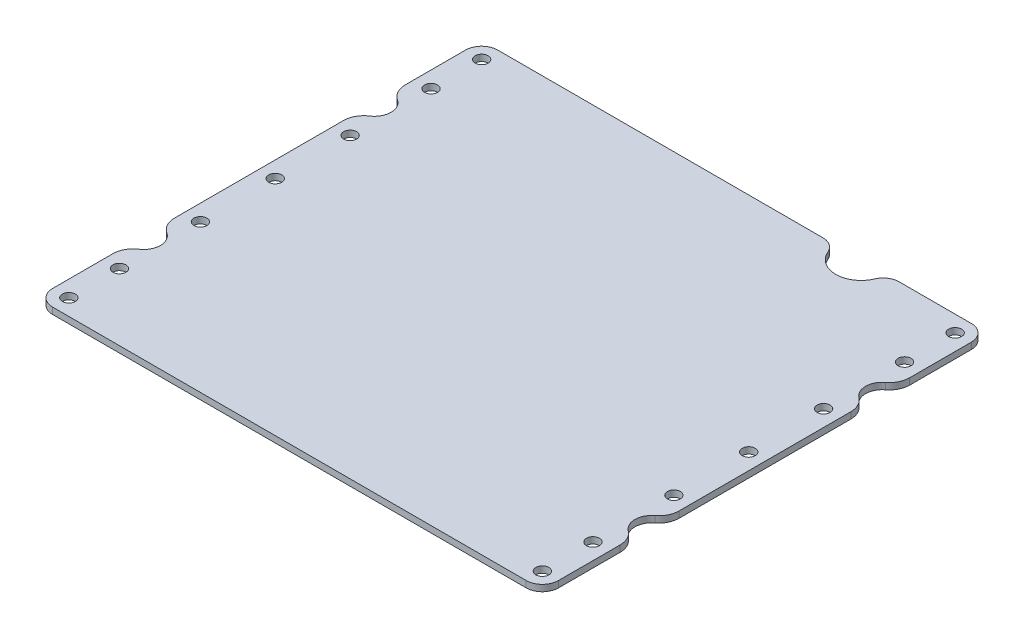
SolidWorks part; units mm, degrees
material "Glass"
ref_plane "Front Plane" through (0, 0, 0) normal (0, 0, 1) x (1, 0, 0)
ref_plane "Top Plane" through (0, 0, 0) normal (0, 1, 0) x (1, 0, 0)
ref_plane "Right Plane" through (0, 0, 0) normal (1, 0, 0) x (0, 0, -1)
sketch "Sketch1" plane through (0, 0, 0) normal (0, 1, 0) x (1, 0, 0)
  line L0 (0, -110) -> (0, 110) construction
  line L1 (-125, 110) -> (125, 110)
  line L2 (-125, 110) -> (-125, -110)
  line L3 (-125, -110) -> (125, -110)
  line L4 (125, 110) -> (125, -110)
  line L5 (0, 0) -> (125, 0) construction
  line L6 (-126.6867, 57) -> (126, 57) construction
  line L7 (-126, -57) -> (103.0564, -57) construction
  dimension "D1" = 250
  dimension "D2" = 220
extrude "Boss-Extrude1" add sketch "Sketch1" along normal blind 3.175
sketch "Sketch2" plane through (0, 3.175, 0) normal (0, 1, 0) x (-1, 0, 0)
  line L0 (0, 0) -> (0, -90.9285) construction
  line L1 (72.0845, 0) -> (-61.4496, 0) construction
  line L2 (117, 102) -> (117, -102) construction
  line L3 (97, 102) -> (97, -102) construction
  line L4 (-97, -102) -> (-97, 102) construction
  line L5 (-117, 102) -> (-117, -102) construction
  line L6 (117, -102) -> (-117, -102) construction
  line L7 (117, 102) -> (-117, 102) construction
  line L8 (-125, -110) -> (125, -110) construction
  line L9 (125, -110) -> (125, 110) construction
  line L10 (126, 57) -> (-134.8366, 57) construction
  circle A0 centre (117, -102) radius 3.2
  circle A1 centre (97, -102) radius 3.2 construction
  circle A2 centre (-97, -102) radius 3.2 construction
  circle A3 centre (-117, -102) radius 3.2
  circle A4 centre (-97, 102) radius 3.2 construction
  circle A5 centre (-117, 102) radius 3.2
  circle A6 centre (117, 102) radius 3.2
  circle A7 centre (97, 102) radius 3.2 construction
  circle A8 centre (117, -77) radius 3.2
  circle A9 centre (117, 77) radius 3.2
  circle A10 centre (-117, 77) radius 3.2
  circle A11 centre (-117, -77) radius 3.2
  circle A12 centre (117, 37) radius 3.2
  circle A13 centre (117, -37) radius 3.2
  circle A14 centre (-117, -37) radius 3.2
  circle A15 centre (-117, 37) radius 3.2
  dimension "D1" = 6.4
  dimension "D2" = 8
  dimension "D3" = 8
  dimension "D4" = 20
  dimension "D5" = 25
extrude "Cut-Extrude1" cut sketch "Sketch2" against normal through all
fillet "Fillet1" radius 8 4 edges at (-125, 1.5875, 110) (125, 1.5875, 110) (125, 1.5875, -110) (-125, 1.5875, -110)
sketch "Sketch4" plane through (0, 3.175, 0) normal (0, 1, 0) x (1, 0, 0)
  line L0 (117, 110) -> (-117, 110) construction
  line L1 (75, 110) -> (50, 110)
  line L2 (125, -102) -> (125, 102) construction
  arc A0 (50, 110) -> (75, 110) centre (62.5, 110) ccw
  dimension "D1" = 25
  dimension "D2" = 50
extrude "Cut-Extrude3" cut sketch "Sketch4" against normal through all
fillet "Fillet3" radius 8 2 edges at (75, 1.5875, -110) (50, 1.5875, -110)
sketch "Sketch5" plane through (0, 3.175, 0) normal (0, 1, 0) x (1, 0, 0)
  line L0 (-125, 57) -> (-117, 57) construction
  line L1 (-117, 77) -> (-117, 37) construction
  line L2 (-125, 102) -> (-125, -102) construction
  line L3 (-125, -57) -> (-116.75, -57) construction
  line L4 (125, -102) -> (125, 102) construction
  line L5 (108.6411, 70.2407) -> (117.7113, 53.1352)
  line L6 (125, -57) -> (115.662, -57) construction
  line L7 (112.3553, -72.0589) -> (111.8223, -72.5919)
  line L8 (108.6411, -70.2407) -> (117.7113, -53.1352)
  line L9 (112.3553, -72.0589) -> (125, -77.2965) construction
  line L10 (125, -77.2965) -> (125, -65.25)
  line L11 (108.3223, -74.6777) -> (126, -57) construction
  line L12 (0, 0) -> (107.8205, 0) construction
  line L13 (112.3553, 72.0589) -> (111.8223, 72.5919)
  line L14 (125, 77.2965) -> (125, 65.25)
  line L19 (108.3223, -74.6777) -> (118.6777, -74.6777) construction
  circle A0 centre (-125, 57) radius 8.25
  circle A1 centre (-125, -57) radius 8.25
  circle A2 centre (-117, -77) radius 3.2 construction
  circle A3 centre (-117, -37) radius 3.2 construction
  arc A4 (111.8223, 72.5919) -> (108.6411, 70.2407) centre (110.4081, 71.1777) ccw
  arc A5 (125, -65.25) -> (117.7113, -53.1352) centre (125, -57) ccw
  circle A8 centre (117, -77) radius 3.2 construction
  circle A9 centre (117, -37) radius 3.2 construction
  arc A10 (111.8223, -72.5919) -> (108.6411, -70.2407) centre (110.4081, -71.1777) cw
  arc A11 (112.3553, -72.0589) -> (125, -77.2965) centre (117.5929, -77.2965) cw
  circle A12 centre (126, -57) radius 4 construction
  arc A13 (112.3553, 72.0589) -> (125, 77.2965) centre (117.5929, 77.2965) ccw
  arc A14 (125, 65.25) -> (117.7113, 53.1352) centre (125, 57) cw
  dimension "D1" = 16.5
  dimension "D2" = 2
  dimension "D4" = 1
  dimension "D3" = 45
  dimension "D5" = 25
  dimension "D6" = 3.5
extrude "Cut-Extrude4" cut sketch "Sketch5" against normal through all
fillet "Fillet4" radius 10 4 edges at (-125, 1.5875, 65.25) (-125, 1.5875, 48.75) (-125, 1.5875, -48.75) (-125, 1.5875, -65.25)
fillet "Fillet5" radius 8 2 edges at (125, 1.5875, 48.75) (125, 1.5875, -48.75)
sketch "Sketch6" plane through (0, 3.175, 0) normal (0, 1, 0) x (1, 0, 0)
  line L0 (125, 65.1892) -> (125, 77.2965)
  line L1 (125, 77.2965) -> (116.6452, 73.2785)
  line L2 (116.6452, 73.2785) -> (108.4081, 79.3907)
  line L3 (108.4081, 79.3907) -> (108.4081, 56.119)
  line L4 (108.4081, 56.119) -> (125, 42.8557)
  line L5 (125, -42.8557) -> (125, 42.8557) construction
  line L6 (125, 42.8557) -> (125, 48.8108)
  line L7 (125, 77.2965) -> (125, 102) construction
  line L8 (0, 0) -> (96.3097, 0) construction
  line L9 (125, -42.8557) -> (125, -48.8108)
  line L10 (108.4081, -56.119) -> (125, -42.8557)
  line L11 (108.4081, -79.3907) -> (108.4081, -56.119)
  line L12 (116.6452, -73.2785) -> (108.4081, -79.3907)
  line L13 (125, -77.2965) -> (116.6452, -73.2785)
  line L14 (125, -65.1892) -> (125, -77.2965)
  arc A0 (125, 65.1892) -> (125, 48.8108) centre (126, 57) ccw
  arc A1 (125, 42.8557) -> (120.9385, 49.819) centre (117, 42.8557) ccw construction
  arc A2 (112.3553, 72.0589) -> (125, 77.2965) centre (117.5929, 77.2965) ccw construction
  arc A3 (125, -48.8108) -> (125, -65.1892) centre (126, -57) ccw
  circle A4 centre (117, 77) radius 3.2 construction
  circle A5 centre (126, -57) radius 4 construction
  arc A6 (111.8223, 72.5919) -> (108.6411, 70.2407) centre (110.4081, 71.1777) ccw construction
  dimension "D1" = 16.5
extrude "Boss-Extrude2" add sketch "Sketch6" against normal up to surface (3.175 mm away) up to face at (26.9744, 0, -12.4953)
fillet "Fillet6" radius 10 4 edges at (125, 1.5875, 65.1892) (125, 1.5875, 48.8108) (125, 1.5875, -65.1892) (125, 1.5875, -48.8108)
sketch "Sketch7" plane through (0, 3.175, 0) normal (0, 1, 0) x (1, 0, 0)
  line L0 (117.0025, -3.2) -> (117.0025, 3.2) construction
  line L1 (119.4645, -3.2) -> (114.5405, -3.2) construction
  line L2 (114.5405, 3.2) -> (119.4645, 3.2) construction
  line L3 (0, 0) -> (0, -80.3554) construction
  circle A0 centre (117.0025, 0) radius 3.2
  circle A1 centre (-117.0025, 0) radius 3.2
extrude "Cut-Extrude5" cut sketch "Sketch7" against normal through all
